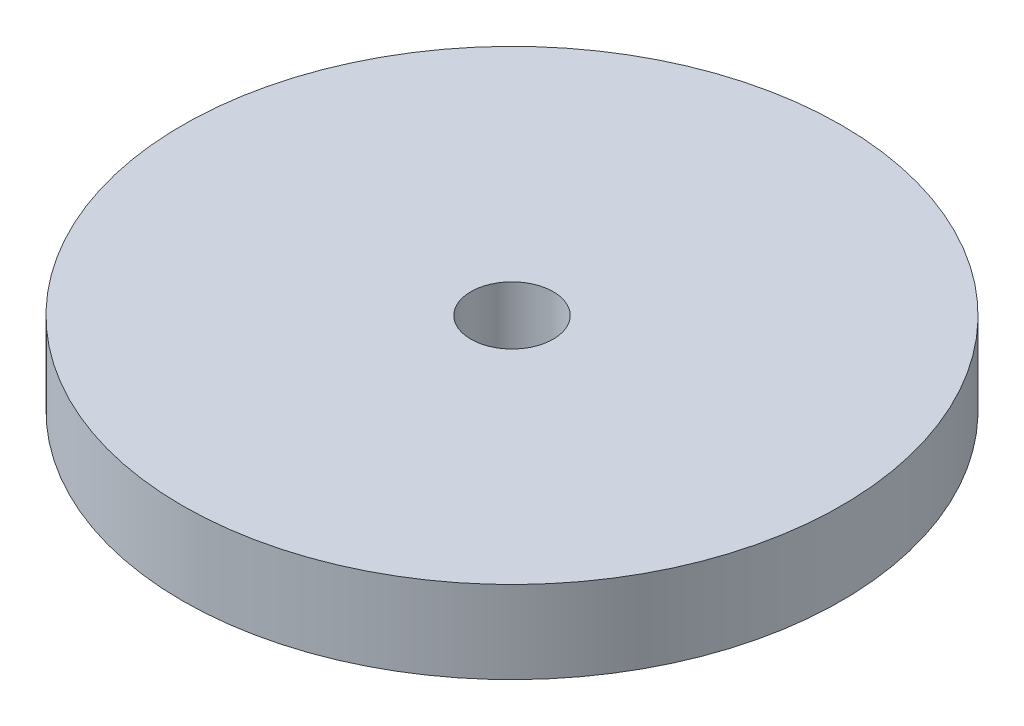
SolidWorks part; units mm, degrees
ref_plane "Front Plane" through (0, 0, 0) normal (0, 0, 1) x (1, 0, 0)
ref_plane "Top Plane" through (0, 0, 0) normal (0, 1, 0) x (1, 0, 0)
ref_plane "Right Plane" through (0, 0, 0) normal (1, 0, 0) x (0, 0, -1)
sketch "Sketch1" plane through (0, 0, 0) normal (0, 1, 0) x (1, 0, 0)
  circle A0 centre (0, 0) radius 25.4
  circle A1 centre (0, 0) radius 3.175
extrude "Boss-Extrude1" add sketch "Sketch1" along normal blind 6.35
